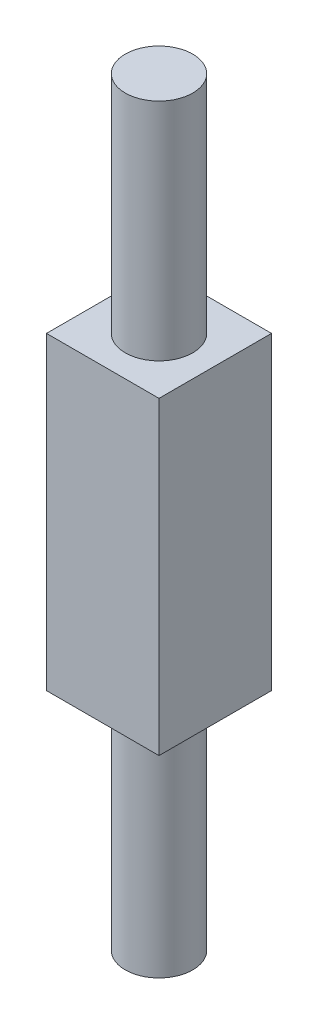
SolidWorks part; units mm, degrees
ref_plane "Front Plane" through (0, 0, 0) normal (0, 0, 1) x (1, 0, 0)
ref_plane "Top Plane" through (0, 0, 0) normal (0, 1, 0) x (1, 0, 0)
ref_plane "Right Plane" through (0, 0, 0) normal (1, 0, 0) x (0, 0, -1)
sketch "Sketch1" plane through (0, 0, 0) normal (0, 1, 0) x (1, 0, 0)
  circle A0 centre (0, 0) radius 1.2
  dimension "D1" = 2.4
extrude "Boss-Extrude1" add sketch "Sketch1" along normal mid plane 27
sketch "Sketch2" plane through (0, 0, 0) normal (0, 1, 0) x (1, 0, 0)
  line L1 (2, -2) -> (-2, -2)
  line L2 (2, -2) -> (2, 2)
  line L3 (2, 2) -> (-2, 2)
  line L4 (-2, -2) -> (-2, 2)
  line L5 (2, -2) -> (-2, 2) construction
  line L6 (2, 2) -> (-2, -2) construction
  point P0 (0, 0)
  point P6 (-1.1369, 1.1369)
  dimension "D1" = 4
extrude "Boss-Extrude2" add sketch "Sketch2" along normal mid plane 11
